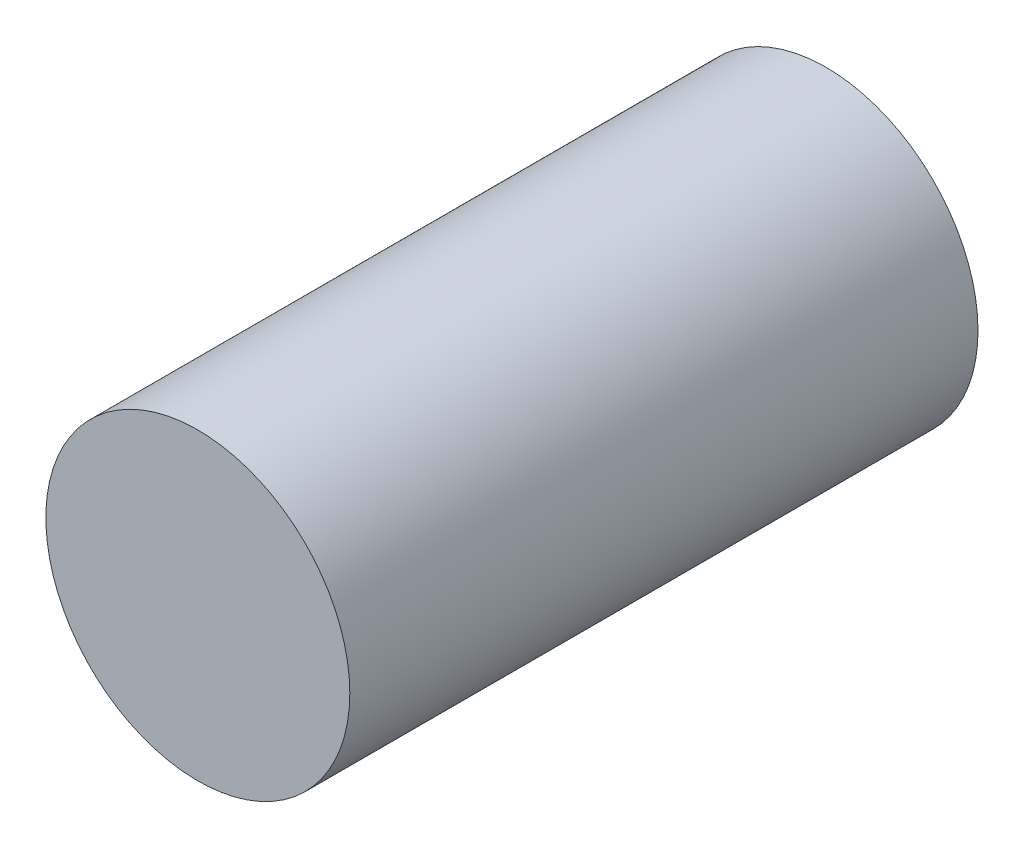
SolidWorks part; units mm, degrees
ref_plane "Front Plane" through (0, 0, 0) normal (0, 0, 1) x (1, 0, 0)
ref_plane "Top Plane" through (0, 0, 0) normal (0, 1, 0) x (1, 0, 0)
ref_plane "Right Plane" through (0, 0, 0) normal (1, 0, 0) x (0, 0, -1)
sketch "Sketch1" plane through (0, 0, 0) normal (0, 0, 1) x (1, 0, 0)
  circle A0 centre (0, 0) radius 15
extrude "Boss-Extrude1" add sketch "Sketch1" along normal mid plane 62
